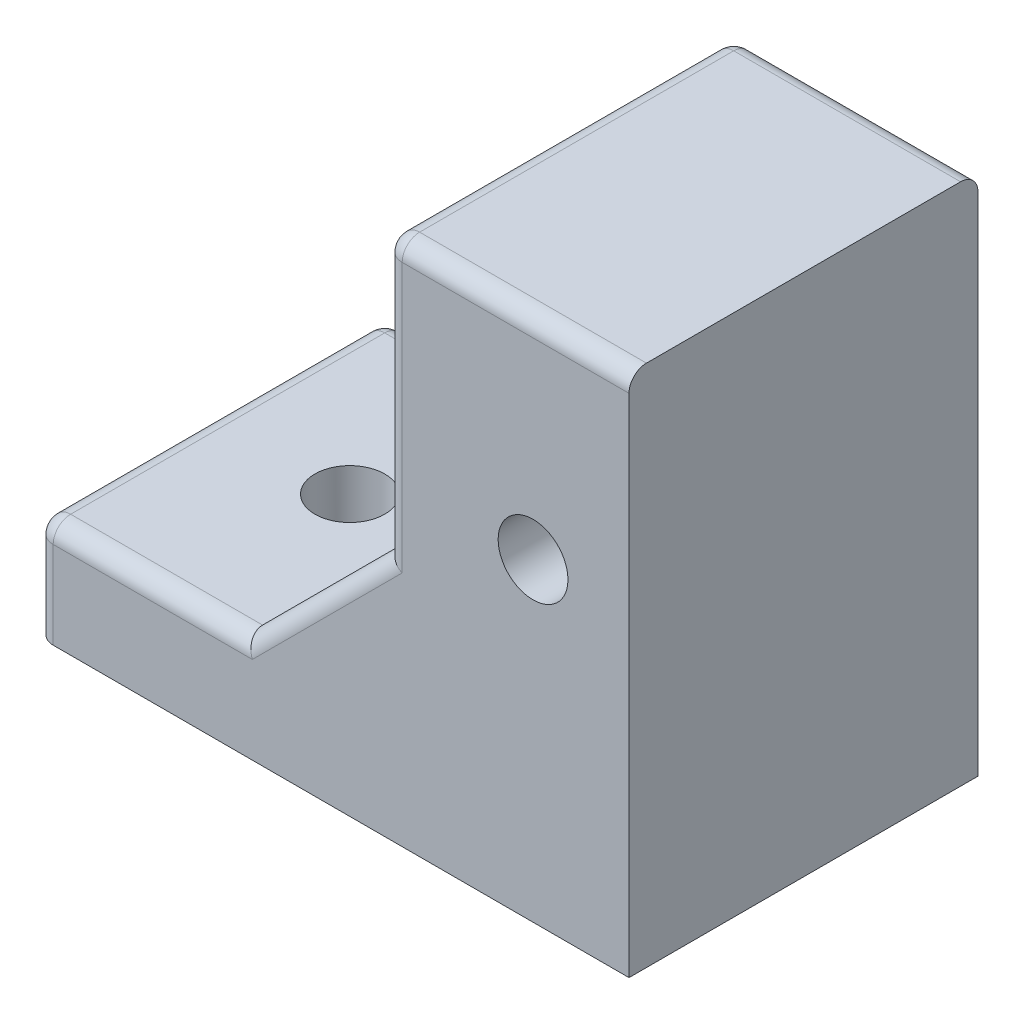
SolidWorks part; units mm, degrees
ref_plane "Plan de face" through (0, 0, 0) normal (0, 0, 1) x (1, 0, 0)
ref_plane "Plan de dessus" through (0, 0, 0) normal (0, 1, 0) x (1, 0, 0)
ref_plane "Plan de droite" through (0, 0, 0) normal (1, 0, 0) x (0, 0, -1)
sketch "Esquisse2" plane through (0, 0, 0) normal (0, 1, 0) x (1, 0, 0)
  line L0 (0, 0) -> (0, 6.3851) construction
  line L1 (-3.5, 5) -> (3.5, 5)
  line L2 (-3.5, 5) -> (-3.5, -5)
  line L3 (-3.5, -5) -> (3.5, -5)
  line L4 (3.5, 5) -> (3.5, -5)
  line L5 (0, 0) -> (8.0113, 0) construction
  dimension "D1" = 7
  dimension "D2" = 10
extrude "Boss.-Extru.1" add sketch "Esquisse2" along normal blind 15 contours L1 L4 L3 L2
sketch "Esquisse3" plane through (-3.5, 0, 0) normal (-1, 0, 0) x (0, 0, 1)
  line L0 (-5, 0) -> (5, 0) construction
  line L1 (-5, 0) -> (5, 0)
  line L2 (-5, 0) -> (-5, 3)
  line L3 (-5, 3) -> (5, 3)
  line L4 (5, 0) -> (5, 3)
  line L5 (5, 15) -> (5, 0) construction
  point P8 (0, 0)
  dimension "D1" = 3
extrude "Boss.-Extru.2" add sketch "Esquisse3" along normal blind 10
sketch "Esquisse6" plane through (0, 0, 5) normal (0, 0, 1) x (1, 0, 0)
  line L0 (-7.5, 3) -> (-3.5, 7)
  line L1 (-13.5, 3) -> (-3.5, 3) construction
  line L2 (-3.5, 15) -> (-3.5, 3) construction
  line L3 (-3.5, 7) -> (-3.5, 3)
  line L4 (-3.5, 3) -> (-7.5, 3)
  dimension "D1" = 45
  dimension "D2" = 4
extrude "Boss.-Extru.3" add sketch "Esquisse6" against normal blind 2
mirror "Symétrie1" about plane through (0, 0, 0) normal (0, 0, 1) of "Boss.-Extru.3"
sketch "Esquisse7" plane through (0, 3, 0) normal (0, 1, 0) x (1, 0, 0)
  line L0 (-13.5, -5) -> (-13.5, 5) construction
  circle A0 centre (-9.5, 0) radius 1
  point P2 (0, 0)
  dimension "D1" = 2
  dimension "D2" = 4
extrude "Enlèv. mat.-Extru.1" cut sketch "Esquisse7" against normal through all both and the other way through all contours A0
sketch "Esquisse8" plane through (0, 0, 5) normal (0, 0, 1) x (1, 0, 0)
  line L1 (3.5, 15) -> (3.5, 0) construction
  circle A0 centre (0.75, 9) radius 1
  point P2 (0, 0)
  point P3 (1.2279, 11.9011)
  dimension "D3" = 2
  dimension "D2" = 2.75
  dimension "D4" = 9
extrude "Enlèv. mat.-Extru.2" cut sketch "Esquisse8" against normal through all both and the other way through all
fillet "Congé1" radius 0.5 12 edges at (-13.5, 1.5, 5) (-13.5, 1.5, -5) (-3.5, 11, -5) (-5.5, 5, -5) (-10.5, 3, -5) (-13.5, 3, 0) (-10.5, 3, 5) (-3.5, 11, 5) (-5.5, 5, 5) (0, 15, -5) (-3.5, 15, 0) (0, 15, 5)
